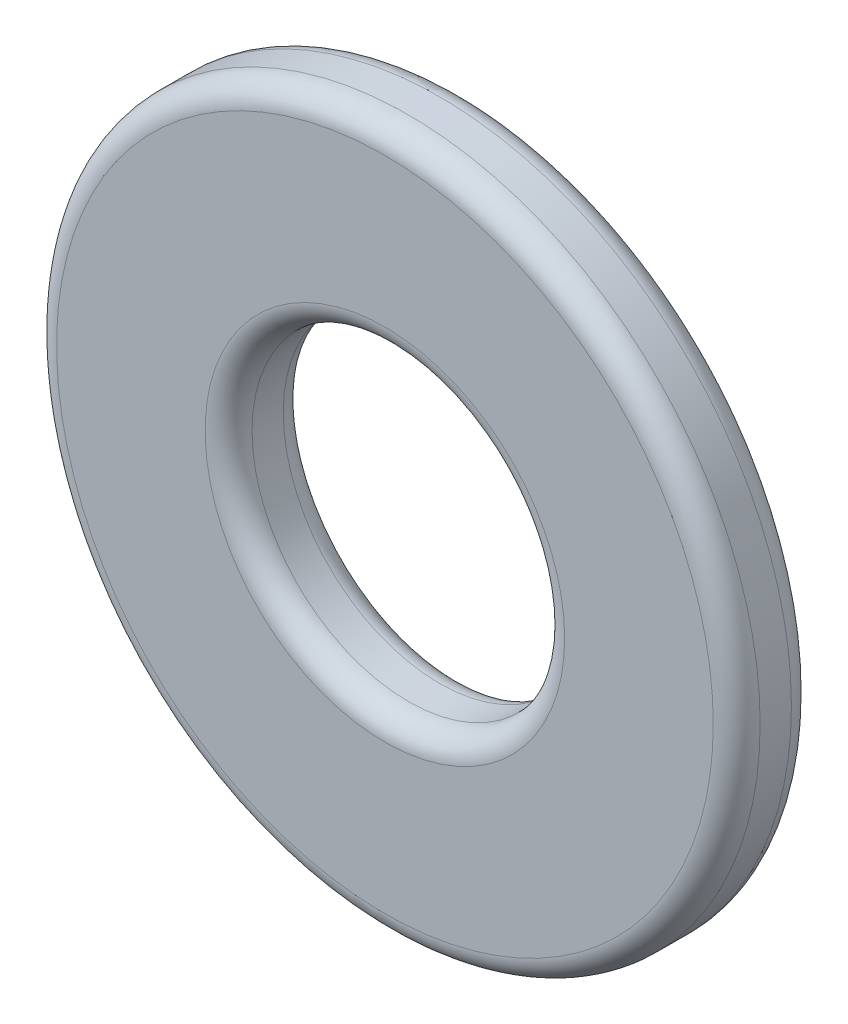
SolidWorks part; units mm, degrees
material "Brass"
ref_plane "Frontal" through (0, 0, 0) normal (0, 0, 1) x (1, 0, 0)
ref_plane "Superior" through (0, 0, 0) normal (0, 1, 0) x (1, 0, 0)
ref_plane "Direito" through (0, 0, 0) normal (1, 0, 0) x (0, 0, -1)
sketch "Sketch1" plane through (0, 0, 0) normal (0, 0, 1) x (1, 0, 0)
  circle A0 centre (0, 0) radius 2.25
  circle A1 centre (0, 0) radius 1
  dimension "D1" = 4.5
  dimension "D2" = 2
extrude "Extrude1" add sketch "Sketch1" along normal mid plane 0.5
fillet "Fillet1" radius 0.15 4 edges at (1, 0, -0.25) (1, 0, 0.25) (2.25, 0, -0.25) (2.25, 0, 0.25)
